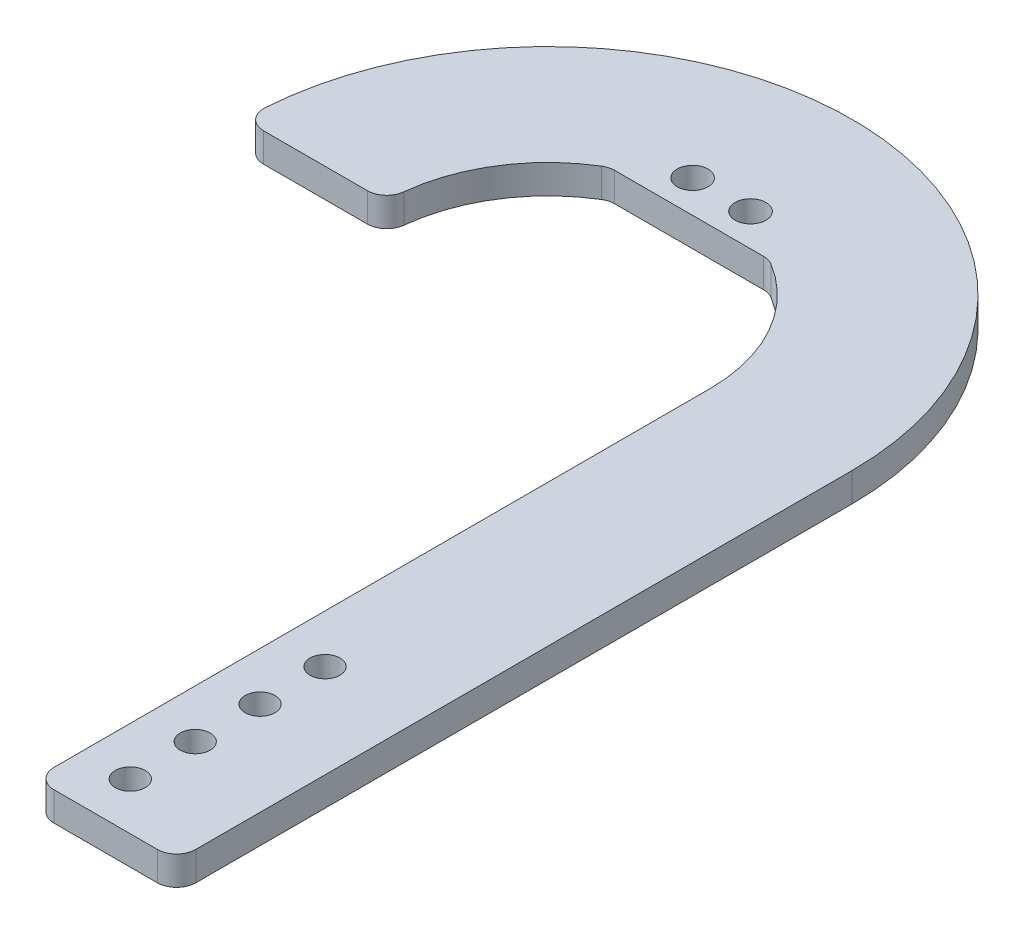
SolidWorks part; units mm, degrees
other "Markup1"
sketch "Sketch3" plane through (-44.7, 3.175, -44.7) normal (0, 1, 0) x (1, 0, 0)
ref_plane "Front Plane" through (0, 0, 0) normal (0, 0, 1) x (1, 0, 0)
ref_plane "Top Plane" through (0, 0, 0) normal (0, 1, 0) x (1, 0, 0)
ref_plane "Right Plane" through (0, 0, 0) normal (1, 0, 0) x (0, 0, -1)
sketch "Sketch2" plane through (0, 0, 0) normal (0, 1, 0) x (1, 0, 0)
  line L0 (16.8134, -70) -> (26.8134, -70)
  line L2 (16.8134, -70) -> (16.8134, 0)
  line L4 (-31.5228, 0) -> (-16.8134, 0)
  line L5 (21.8134, -65.0887) -> (21.8134, -58.3629) construction
  line L6 (-8.2731, 14.6371) -> (8.2731, 14.6371)
  line L7 (-3, 18) -> (3, 18) construction
  line L8 (21.8134, -58.3629) -> (21.8134, -51.6371) construction
  line L9 (21.8134, -51.6371) -> (21.8134, -44.9113) construction
  line L10 (26.8134, -70) -> (26.8134, -40)
  line L11 (26.8134, -40) -> (31.5228, 0)
  line L12 (31.5228, 0) -> (31.5228, -70)
  line L13 (31.5228, -70) -> (26.8134, -70)
  arc A0 (31.5228, 0) -> (-31.5228, 0) centre (0, 0) ccw
  arc A1 (16.8134, 0) -> (-16.8134, 0) centre (0, 0) ccw
  circle A2 centre (21.8134, -65.0887) radius 1.55
  circle A3 centre (21.8134, -58.3629) radius 1.55
  circle A4 centre (-3, 18) radius 1.6
  circle A5 centre (3, 18) radius 1.6
  circle A6 centre (21.8134, -51.6371) radius 1.55
  circle A7 centre (21.8134, -44.9113) radius 1.55
  point P17 (21.8134, -70)
  point P19 (0, 18)
  dimension "D4" = 3.1
  dimension "D5" = 16.5463
  dimension "D8" = 16.8134
  dimension "D9" = 3.2
  dimension "D2" = 31.5228
  dimension "D3" = 6.7258
  dimension "D6" = 4.9113
  dimension "D7" = 18
  dimension "D10" = 6
  dimension "D11" = 10
  dimension "D12" = 30
  dimension "D13" = 70
extrude "Boss-Extrude1" add sketch "Sketch2" along normal blind 3
fillet "Fillet1" radius 2 6 edges at (8.2731, 1.5, -14.6371) (-8.2731, 1.5, -14.6371) (31.5228, 1.5, 70) (16.8134, 1.5, 70) (-16.8134, 1.5, 0) (-31.5228, 1.5, 0)
